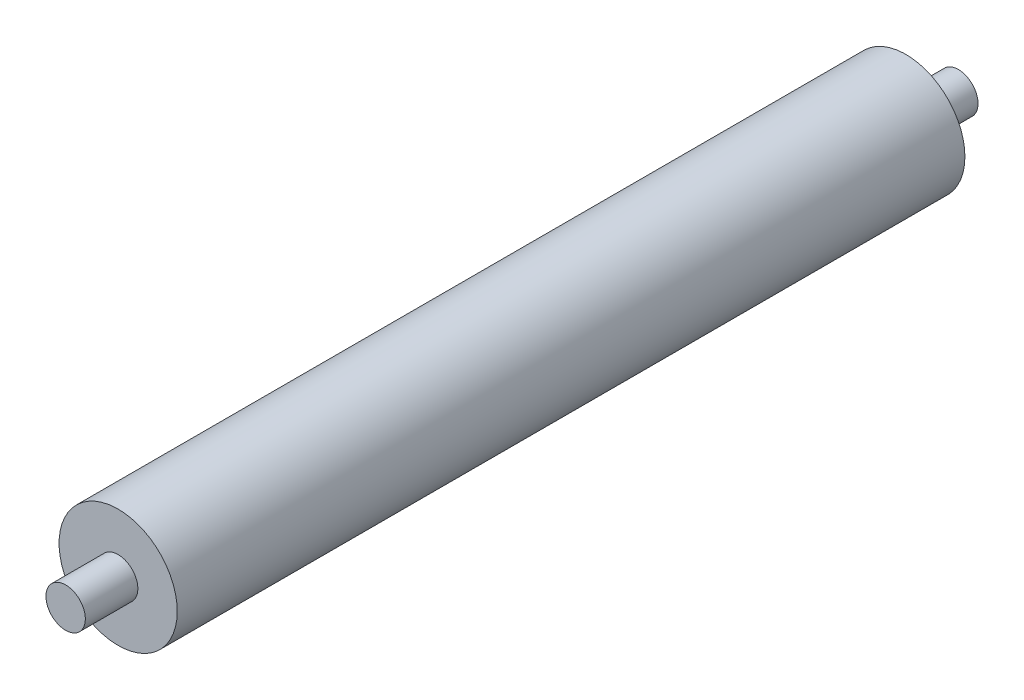
SolidWorks part; units mm, degrees
ref_plane "Front Plane" through (0, 0, 0) normal (0, 0, 1) x (1, 0, 0)
ref_plane "Top Plane" through (0, 0, 0) normal (0, 1, 0) x (1, 0, 0)
ref_plane "Right Plane" through (0, 0, 0) normal (1, 0, 0) x (0, 0, -1)
sketch "Sketch1" plane through (0, 0, 0) normal (0, 0, 1) x (1, 0, 0)
  circle A0 centre (0, 0) radius 22.5
  dimension "D1" = 45
extrude "Boss-Extrude1" add sketch "Sketch1" along normal blind 300
sketch "Sketch2" plane through (0, 0, 300) normal (0, 0, 1) x (1, 0, 0)
  circle A0 centre (0, 0) radius 7.5
  dimension "D1" = 15
extrude "Boss-Extrude2" add sketch "Sketch2" along normal blind 20
sketch "Sketch3" plane through (0, 0, 0) normal (0, 0, -1) x (-1, 0, 0)
  circle A0 centre (0, 0) radius 7.5
  dimension "D1" = 15
extrude "Boss-Extrude3" add sketch "Sketch3" along normal blind 20
